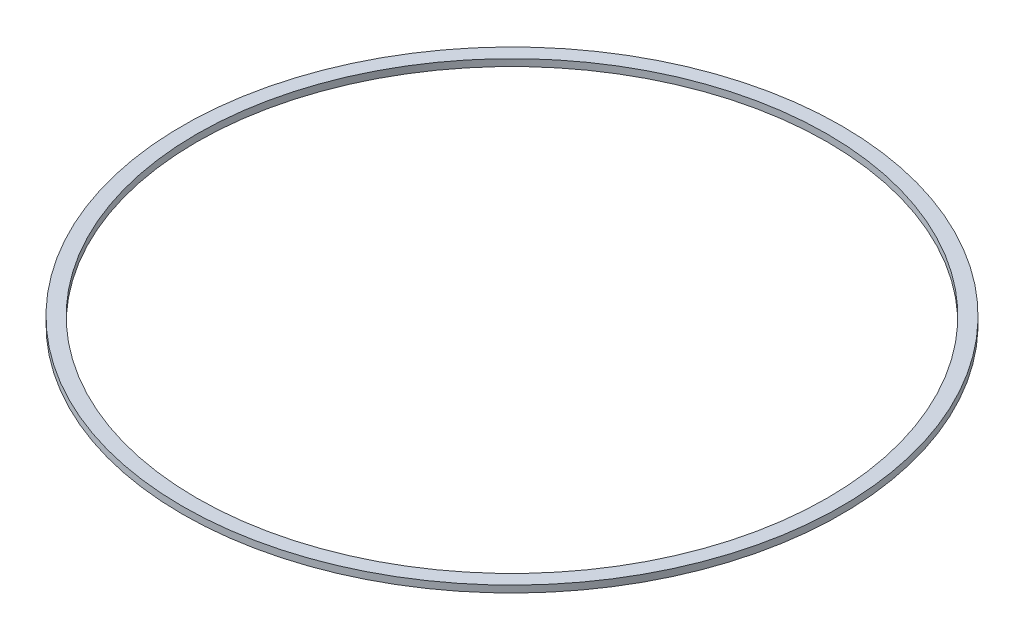
SolidWorks part; units mm, degrees
ref_plane "Front Plane" through (0, 0, 0) normal (0, 0, 1) x (1, 0, 0)
ref_plane "Top Plane" through (0, 0, 0) normal (0, 1, 0) x (1, 0, 0)
ref_plane "Right Plane" through (0, 0, 0) normal (1, 0, 0) x (0, 0, -1)
sketch "Sketch2" plane through (0, 0, 0) normal (0, 0, 1) x (1, 0, 0)
  line L0 (-55.2, -0.2) -> (-52.5, -0.2)
  line L1 (0, 0) -> (-55, 0)
  line L2 (0, 0) -> (0, 8.1)
  line L3 (0, 8.1) -> (-55, 8.1)
  line L4 (-55, 0) -> (-55, 8.1)
  line L5 (-52.5, -0.2) -> (-52.5, -3.2)
  line L6 (-52.5, -3.2) -> (-63.2, -3.2)
  line L7 (-63.2, -3.2) -> (-63.2, 11.8)
  line L12 (-55.2, 11.8) -> (-55.2, -0.2)
  line L13 (-55.2, 11.8) -> (-63.2, 11.8)
  line L14 (0, 0) -> (0, 30.013) construction
sketch "Sketch3" plane through (0, 0, 0) normal (0, 0, 1) x (1, 0, 0)
  line L1 (-55, 9.3) -> (-52.5, 9.3)
  line L2 (-55, 9.3) -> (-55, 8.1)
  line L3 (-55, 8.1) -> (-52.5, 8.1)
  line L4 (-52.5, 9.3) -> (-52.5, 8.1)
sketch "Sketch4" plane through (0, 0, 0) normal (0, 0, 1) x (1, 0, 0)
  line L0 (-55.2, 11.8) -> (-55.2, -0.2) construction
  line L1 (-55.2, 9.3) -> (-57.7, 9.3)
  line L2 (-55.2, 9.3) -> (-55.2, 8.1)
  line L3 (-55.2, 8.1) -> (-57.7, 8.1)
  line L4 (-57.7, 9.3) -> (-57.7, 8.1)
  line L5 (0, 0) -> (0, 13.6575) construction
  line L6 (0, 8.1) -> (-55, 8.1) construction
  line L7 (-55, 9.3) -> (-52.5, 9.3) construction
revolve "Revolve1" add sketch "Sketch4" angle 360 about L5
